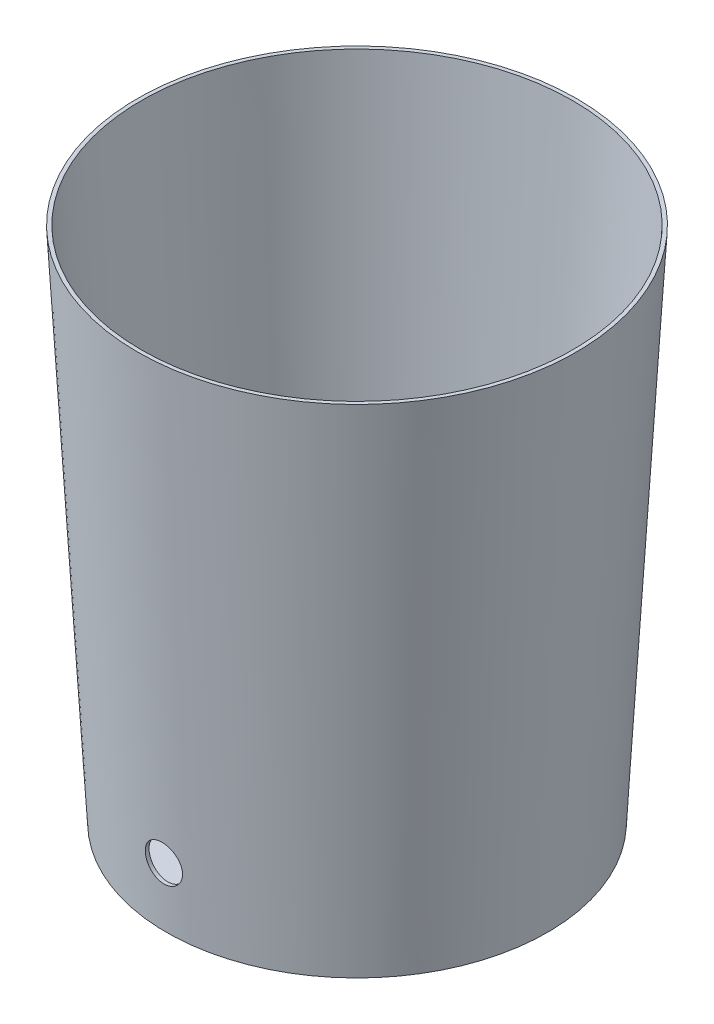
SolidWorks part; units mm, degrees
material "PE High Density"
ref_plane "Front Plane" through (0, 0, 0) normal (0, 0, 1) x (1, 0, 0)
ref_plane "Top Plane" through (0, 0, 0) normal (0, 1, 0) x (1, 0, 0)
ref_plane "Right Plane" through (0, 0, 0) normal (1, 0, 0) x (0, 0, -1)
sketch "Sketch1" plane through (0, 0, 0) normal (0, 0, 1) x (1, 0, 0)
  line L0 (0, 0) -> (0, 353.06)
  line L1 (0, 353.06) -> (149.86, 353.06)
  line L2 (149.86, 353.06) -> (130.048, 0)
  line L3 (130.048, 0) -> (0, 0)
  dimension "D1" = 149.86
  dimension "D2" = 130.048
  dimension "D3" = 353.06
revolve "Revolve1" add sketch "Sketch1" angle 360 about L0
shell "Shell1" thickness 2.54
sketch "Sketch2" plane through (0, 0, 0) normal (0, 0, 1) x (1, 0, 0)
  circle A0 centre (0, 42.1729) radius 12.7
  dimension "D1" = 25.4
extrude "Cut-Extrude1" cut sketch "Sketch2" along normal up to next
equation "\"D2@Sketch1\"=10.24/2"
